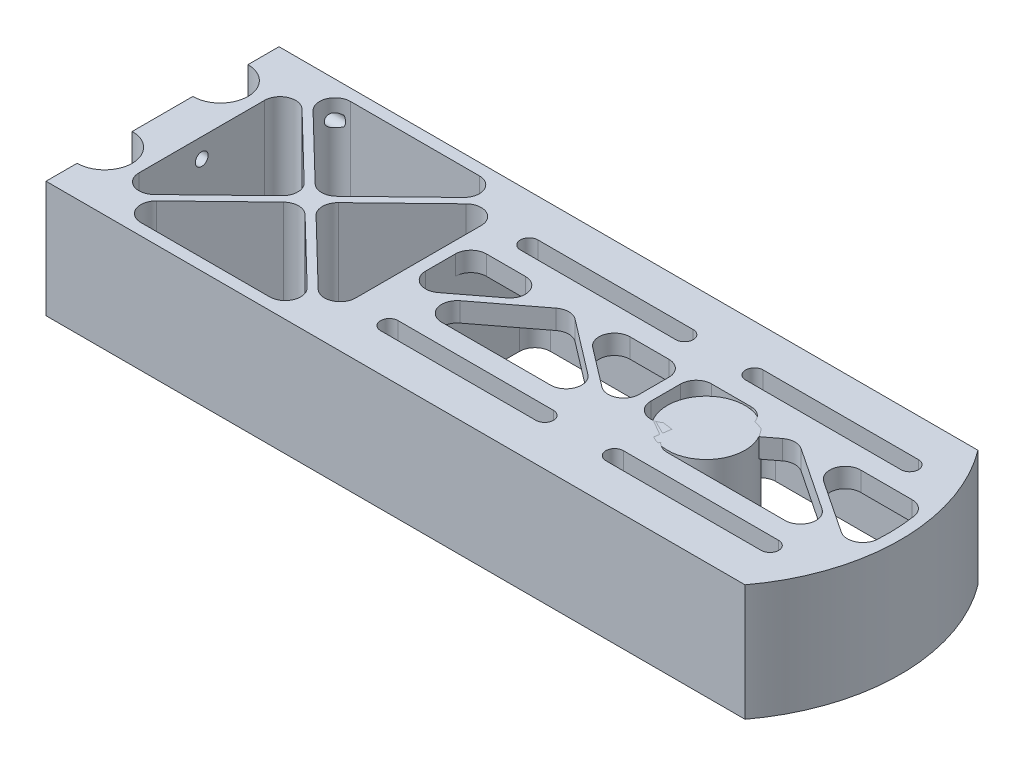
SolidWorks part; units mm, degrees
material "3.1355 (EN-AW 2024)"
ref_plane "Front" through (0, 0, 0) normal (0, 0, 1) x (1, 0, 0)
ref_plane "Top" through (0, 0, 0) normal (0, 1, 0) x (1, 0, 0)
ref_plane "Right" through (0, 0, 0) normal (1, 0, 0) x (0, 0, -1)
sketch "Эскиз1" plane through (0, 0, 0) normal (0, 1, 0) x (1, 0, 0)
  line L0 (0, 0) -> (0, 60) construction
  line L1 (0, 60) -> (180, 60)
  line L2 (190, 60) -> (190, 0) construction
  line L3 (190, 0) -> (180, 0) construction
  line L4 (0, 30) -> (140, 30) construction
  line L5 (0, 60) -> (0, 52)
  line L6 (0, 37.8) -> (0, 22.2)
  line L7 (0, 8) -> (0, 0)
  line L8 (140, 30) -> (190, 30) construction
  line L9 (180, 60) -> (190, 60) construction
  line L10 (180, 0) -> (0, 0)
  circle A0 centre (0, 44.9) radius 7.1 construction
  circle A1 centre (0, 15.1) radius 7.1 construction
  arc A2 (0, 52) -> (0, 37.8) centre (0, 44.9) cw
  arc A3 (0, 8) -> (0, 22.2) centre (0, 15.1) ccw
  arc A4 (180, 0) -> (180, 60) centre (140, 30) ccw
  point P11 (0, 52)
  point P12 (0, 37.8)
  dimension "D2" = 14.2
  dimension "D4" = 29.8
  dimension "D8" = 50
  dimension "D1" = 60
  dimension "D3" = 15.1
  dimension "D5" = 140
  dimension "D6" = 50
  dimension "D7" = 190
extrude "Бобышка-Вытянуть1" add sketch "Эскиз1" along normal blind 30
sketch "Эскиз2" plane through (0, 30, 0) normal (0, 1, 0) x (1, 0, 0)
  line L5 (3, 3) -> (178.4708, 3)
  line L6 (3, 3) -> (178.4708, 3)
  line L12 (3, 5.4558) -> (3, 3)
  line L15 (178.4708, 57) -> (3, 57)
  line L16 (3, 57) -> (3, 54.5442)
  line L17 (3, 35.2558) -> (3, 24.7442)
  line L18 (3, 5.4558) -> (3, 3)
  line L21 (178.4708, 57) -> (3, 57)
  line L22 (3, 57) -> (3, 54.5442)
  line L23 (3, 35.2558) -> (3, 24.7442)
  arc A3 (178.4708, 3) -> (178.4708, 57) centre (140, 30) ccw
  arc A4 (3, 35.2558) -> (3, 54.5442) centre (0, 44.9) ccw
  arc A5 (3, 5.4558) -> (3, 24.7442) centre (0, 15.1) ccw
  arc A6 (3, 35.2558) -> (3, 54.5442) centre (0, 44.9) ccw
  arc A7 (3, 5.4558) -> (3, 24.7442) centre (0, 15.1) ccw
  arc A8 (178.4708, 3) -> (178.4708, 57) centre (140, 30) ccw
  dimension "D1" = 3
extrude "Вырез-Вытянуть1" cut sketch "Эскиз2" against normal through all
sketch "Temp" plane through (0, 30, 0) normal (0, 1, 0) x (1, 0, 0)
  circle A0 centre (140, 30) radius 10
  dimension "D1" = 20
extrude "Бобышка-Вытянуть2" add sketch "Temp" against normal up to surface (30 mm away) separate body up to face at (49.7088, 0, -30)
sketch "Эскиз3" plane through (0, 30, 0) normal (0, 1, 0) x (1, 0, 0)
  line L0 (178.4708, 57) -> (3, 57) construction
  line L1 (174.4166, 48) -> (134.4166, 48) construction
  line L2 (174.4166, 43.5) -> (134.4166, 43.5)
  line L3 (174.4166, 52.5) -> (134.4166, 52.5)
  line L4 (174.4166, 48) -> (183.4166, 48) construction
  line L5 (125.4166, 57) -> (125.4166, 30) construction
  line L6 (0, 30) -> (140, 30) construction
  line L7 (76.4166, 48) -> (116.4166, 48) construction
  line L8 (76.4166, 43.5) -> (116.4166, 43.5)
  line L9 (76.4166, 52.5) -> (116.4166, 52.5)
  line L10 (187, 30) -> (125.4166, 30) construction
  line L11 (76.4166, 12) -> (116.4166, 12) construction
  line L12 (76.4166, 16.5) -> (116.4166, 16.5)
  line L13 (76.4166, 7.5) -> (116.4166, 7.5)
  line L14 (174.4166, 12) -> (134.4166, 12) construction
  line L15 (174.4166, 16.5) -> (134.4166, 16.5)
  line L16 (174.4166, 7.5) -> (134.4166, 7.5)
  line L17 (68.9166, 57) -> (68.9166, 40.5)
  line L18 (68.9166, 40.5) -> (185.8121, 40.5)
  line L19 (178.4708, 57) -> (68.9166, 57)
  line L20 (76.4166, 12) -> (116.4166, 12) construction
  line L21 (76.4166, 16.5) -> (116.4166, 16.5)
  line L22 (76.4166, 7.5) -> (116.4166, 7.5)
  line L23 (174.4166, 12) -> (134.4166, 12) construction
  line L24 (174.4166, 16.5) -> (134.4166, 16.5)
  line L25 (174.4166, 7.5) -> (134.4166, 7.5)
  line L26 (68.9166, 19.5) -> (185.8121, 19.5)
  line L27 (178.4708, 3) -> (68.9166, 3)
  line L28 (68.9166, 3) -> (68.9166, 19.5)
  arc A0 (174.4166, 43.5) -> (174.4166, 52.5) centre (174.4166, 48) ccw
  arc A1 (134.4166, 52.5) -> (134.4166, 43.5) centre (134.4166, 48) ccw
  arc A2 (178.4708, 3) -> (178.4708, 57) centre (140, 30) ccw construction
  arc A3 (76.4166, 43.5) -> (76.4166, 52.5) centre (76.4166, 48) cw
  arc A4 (116.4166, 52.5) -> (116.4166, 43.5) centre (116.4166, 48) cw
  arc A5 (76.4166, 16.5) -> (76.4166, 7.5) centre (76.4166, 12) ccw
  arc A6 (116.4166, 7.5) -> (116.4166, 16.5) centre (116.4166, 12) ccw
  arc A7 (174.4166, 16.5) -> (174.4166, 7.5) centre (174.4166, 12) cw
  arc A8 (134.4166, 7.5) -> (134.4166, 16.5) centre (134.4166, 12) cw
  arc A9 (185.8121, 40.5) -> (178.4708, 57) centre (140, 30) ccw
  arc A10 (76.4166, 16.5) -> (76.4166, 7.5) centre (76.4166, 12) ccw
  arc A11 (116.4166, 7.5) -> (116.4166, 16.5) centre (116.4166, 12) ccw
  arc A12 (174.4166, 16.5) -> (174.4166, 7.5) centre (174.4166, 12) cw
  arc A13 (134.4166, 7.5) -> (134.4166, 16.5) centre (134.4166, 12) cw
  arc A14 (185.8121, 19.5) -> (178.4708, 3) centre (140, 30) cw
  point P1 (154.4166, 48)
  point P20 (96.4166, 48)
  point P28 (96.4166, 12)
  point P35 (154.4166, 12)
  arc M3 (178.4708, 57) -> (178.4708, 3) centre (140, 30) cw
  line M4 (178.4708, 3) -> (3, 3)
  line M10 (3, 57) -> (178.4708, 57)
  dimension "D1" = 4.5
  dimension "D6" = 3
  dimension "D2" = 40
  dimension "D3" = 9
  dimension "D4" = 9
  dimension "D5" = 9
  dimension "D7" = 7.5
extrude "Бобышка-Вытянуть3" add sketch "Эскиз3" against normal blind 5 contours L17 L18 A1 L3 A0 L2 L9 A4 L8 A3 M3 M10 | L28 L26 A6 L13 A5 L12 L16 A8 L15 A7 M4 M3
sketch "Эскиз4" plane through (0, 30, 0) normal (0, 1, 0) x (1, 0, 0)
  line L0 (3, 57) -> (3, 54.5442) construction
  line L1 (3, 35.2558) -> (3, 24.7442) construction
  line L2 (3, 5.4558) -> (3, 3) construction
  line L3 (3, 3) -> (68.9166, 3) construction
  line L4 (68.9166, 57) -> (3, 57) construction
  line L5 (3, 57) -> (3, 54.5442)
  line L6 (3, 35.2558) -> (3, 24.7442)
  line L7 (3, 5.4558) -> (3, 3)
  line L8 (3, 3) -> (10.1, 3)
  line L9 (10.1, 57) -> (3, 57)
  line L10 (10.1, 57) -> (10.1, 3)
  arc A0 (3, 35.2558) -> (3, 54.5442) centre (0, 44.9) ccw construction
  arc A1 (3, 5.4558) -> (3, 24.7442) centre (0, 15.1) ccw construction
  arc A2 (3, 35.2558) -> (3, 54.5442) centre (0, 44.9) ccw
  arc A3 (3, 5.4558) -> (3, 24.7442) centre (0, 15.1) ccw
  line M4 (68.9166, 3) -> (3, 3)
  line M5 (3, 3) -> (3, 5.4558)
  arc M6 (3, 5.4558) -> (3, 24.7442) centre (0, 15.1) ccw
  line M7 (3, 24.7442) -> (3, 35.2558)
  arc M8 (3, 35.2558) -> (3, 54.5442) centre (0, 44.9) ccw
  line M9 (3, 54.5442) -> (3, 57)
  line M10 (3, 57) -> (68.9166, 57)
extrude "Бобышка-Вытянуть4" add sketch "Эскиз4" against normal through all contours L10 M10 M9 M8 | L10 M8 M7 M6 | L10 M6 M5 M4
sketch "Эскиз6" plane through (0, 30, 0) normal (0, 1, 0) x (1, 0, 0)
  line L0 (65.9166, 57) -> (65.9166, 3)
  line L1 (68.9166, 57) -> (10.1, 57) construction
  line L2 (10.1, 3) -> (68.9166, 3) construction
  line L3 (68.9166, 57) -> (68.9166, 40.5) construction
  line L4 (65.9166, 3) -> (68.9166, 3)
  line L5 (68.9166, 3) -> (68.9166, 57)
  line L6 (68.9166, 57) -> (65.9166, 57)
  dimension "D1" = 3
extrude "Бобышка-Вытянуть5" add sketch "Эскиз6" against normal through all
sketch "Эскиз7" plane through (0, 30, 0) normal (0, 1, 0) x (1, 0, 0)
  line L0 (10.1, 3) -> (65.9166, 57) construction
  line L1 (10.1, 57) -> (65.9166, 3) construction
  line L2 (10.1, 55.6086) -> (36.5701, 30)
  line L3 (11.5382, 3) -> (38.0083, 28.6086)
  line L4 (11.5382, 57) -> (38.0083, 31.3914)
  line L5 (10.1, 4.3914) -> (36.5701, 30)
  line L6 (65.9166, 57) -> (10.1, 57) construction
  line L7 (10.1, 57) -> (10.1, 3) construction
  line L8 (10.1, 3) -> (65.9166, 3) construction
  line L9 (65.9166, 57) -> (65.9166, 3) construction
  line L10 (65.9166, 57) -> (64.4784, 57)
  line L11 (10.1, 57) -> (10.1, 55.6086)
  line L12 (10.1, 3) -> (11.5382, 3)
  line L13 (65.9166, 57) -> (65.9166, 55.6086)
  line L14 (11.5382, 57) -> (10.1, 57)
  line L15 (10.7953, 57.7187) -> (66.6119, 3.7187) construction
  line L16 (9.4047, 56.2813) -> (65.2213, 2.2813) construction
  line L17 (65.9166, 4.3914) -> (65.9166, 3)
  line L18 (9.4047, 3.7187) -> (65.2213, 57.7187) construction
  line L19 (10.7953, 2.2813) -> (66.6119, 56.2813) construction
  line L20 (64.4784, 3) -> (65.9166, 3)
  line L21 (10.1, 4.3914) -> (10.1, 3)
  line L22 (39.4465, 30) -> (65.9166, 55.6086)
  line L23 (39.4465, 30) -> (65.9166, 4.3914)
  line L24 (38.0083, 31.3914) -> (64.4784, 57)
  line L25 (38.0083, 28.6086) -> (64.4784, 3)
  dimension "D1" = 1
  dimension "D2" = 1
extrude "Бобышка-Вытянуть6" add sketch "Эскиз7" against normal through all
sketch "Эскиз9" plane through (0, 25, 0) normal (0, -1, 0) x (1, 0, 0)
  line L0 (120.9166, -12) -> (129.9166, -12) construction
  line L1 (125.4166, -3) -> (125.4166, -57) construction
  line L2 (68.9166, -57) -> (178.4708, -57) construction
  line L3 (123.9166, -3) -> (123.9166, -57)
  line L4 (101.5292, -3) -> (68.9166, -3) construction
  line L5 (126.9166, -3) -> (126.9166, -57)
  line L6 (123.9166, -3) -> (126.9166, -3)
  line L7 (123.9166, -57) -> (126.9166, -57)
  arc A0 (116.4166, -16.5) -> (116.4166, -7.5) centre (116.4166, -12) ccw construction
  arc A1 (134.4166, -16.5) -> (134.4166, -7.5) centre (134.4166, -12) ccw construction
  point P8 (125.4166, -12)
  dimension "D1" = 1.5
  dimension "D2" = 1.5
extrude "Бобышка-Вытянуть8" add sketch "Эскиз9" along normal through all and the other way through all
sketch "Эскиз8" plane through (0, 30, 0) normal (0, 1, 0) x (1, 0, 0)
  line L0 (96.4166, 43.5) -> (96.4166, 16.5) construction
  line L1 (76.4166, 43.5) -> (116.4166, 43.5) construction
  line L2 (76.4166, 16.5) -> (116.4166, 16.5) construction
  line L3 (154.4166, 43.5) -> (154.4166, 16.5) construction
  line L4 (174.4166, 43.5) -> (134.4166, 43.5) construction
  line L5 (174.4166, 16.5) -> (134.4166, 16.5) construction
  line L6 (68.9166, 19.5) -> (96.4166, 40.5) construction
  line L7 (116.4166, 48) -> (134.4166, 48) construction
  line L8 (125.4166, 48) -> (125.4166, 19.5) construction
  line L9 (68.9166, 40.5) -> (123.9166, 40.5) construction
  line L10 (96.4166, 40.5) -> (123.9166, 19.5) construction
  line L11 (126.9166, 19.5) -> (154.4401, 40.4052) construction
  line L12 (154.4401, 40.4052) -> (185.8121, 19.5) construction
  line L13 (70.5643, 19.5) -> (96.4166, 39.2418)
  line L14 (96.4166, 39.2418) -> (122.2689, 19.5)
  line L15 (128.5699, 19.5) -> (154.478, 39.1782)
  line L16 (154.478, 39.1782) -> (184.0088, 19.5)
  line L17 (68.9166, 20.7582) -> (94.7689, 40.5)
  line L18 (98.0643, 40.5) -> (123.9166, 20.7582)
  line L19 (126.9166, 20.7557) -> (152.9116, 40.5)
  line L20 (122.2689, 19.5) -> (123.9166, 19.5)
  line L22 (94.7689, 40.5) -> (98.0643, 40.5)
  line L23 (68.9166, 19.5) -> (68.9166, 40.5) construction
  line L24 (68.9166, 19.5) -> (123.9166, 19.5) construction
  line L25 (123.9166, 19.5) -> (123.9166, 40.5) construction
  line L26 (126.9166, 40.5) -> (126.9166, 19.5) construction
  line L27 (126.9166, 40.5) -> (185.8121, 40.5) construction
  line L28 (126.9166, 19.5) -> (185.8121, 19.5) construction
  line L29 (68.9166, 19.5) -> (68.9166, 20.7582)
  line L30 (68.9166, 19.5) -> (70.5643, 19.5)
  line L31 (123.9166, 19.5) -> (123.9166, 20.7582)
  line L32 (126.9166, 20.7557) -> (126.9166, 19.5)
  line L33 (152.9116, 40.5) -> (156.1011, 40.5)
  line L34 (126.9166, 19.5) -> (128.5699, 19.5)
  line L35 (184.0088, 19.5) -> (185.8121, 19.5)
  line L36 (154.4021, 41.6321) -> (186.3666, 20.3322) construction
  line L37 (154.478, 39.1782) -> (185.2576, 18.6678) construction
  line L38 (156.1011, 40.5) -> (186.0401, 20.5497)
  line L39 (127.5214, 18.7037) -> (154.478, 39.1782) construction
  line L40 (126.3117, 20.2963) -> (154.4021, 41.6321) construction
  line L42 (96.4166, 41.7582) -> (124.5235, 20.2948) construction
  line L43 (68.3097, 20.2948) -> (96.4166, 41.7582) construction
  line L44 (69.5235, 18.7052) -> (96.4166, 39.2418) construction
  line L45 (96.4166, 39.2418) -> (123.3097, 18.7052) construction
  arc A1 (185.8121, 19.5) -> (185.8121, 40.5) centre (140, 30) ccw construction
  arc A2 (185.8121, 19.5) -> (186.0401, 20.5497) centre (140, 30) ccw
  point P26 (69.5235, 18.7052)
  point P27 (96.4324, 39.2539)
  point P28 (125.4324, 18.2539)
  point P30 (185.2357, 18.6828)
  point P31 (68.3097, 20.2948)
  point P32 (96.4007, 41.7461)
  point P33 (125.4007, 20.7461)
  point P34 (154.3931, 42.8858)
  point P35 (186.3885, 20.3172)
  point P49 (154.4166, 40.5)
  dimension "D1" = 1
  dimension "D2" = 1
extrude "Бобышка-Вытянуть7" add sketch "Эскиз8" against normal up to surface (5 mm away) up to face at (96.4166, 25, -12)
fillet "Скругление1" radius 4 12 edges at (11.5382, 15, -57) (38.0083, 15, -31.3914) (64.4784, 15, -57) (65.9166, 15, -55.6086) (39.4465, 15, -30) (65.9166, 15, -4.3914) (11.5382, 15, -3) (64.4784, 15, -3) (38.0083, 15, -28.6086) (10.1, 15, -4.3914) (36.5701, 15, -30) (10.1, 15, -55.6086)
fillet "Скругление2" radius 4 8 edges at (178.4708, 12.5, -57) (178.4708, 12.5, -3) (126.9166, 12.5, -3) (126.9166, 12.5, -57) (123.9166, 12.5, -3) (68.9166, 12.5, -3) (68.9166, 12.5, -57) (123.9166, 12.5, -57)
fillet "Скругление3" radius 4 18 edges at (98.0643, 27.5, -40.5) (123.9166, 27.5, -40.5) (123.9166, 27.5, -20.7582) (122.2689, 27.5, -19.5) (96.4166, 27.5, -39.2418) (70.5643, 27.5, -19.5) (94.7689, 27.5, -40.5) (68.9166, 27.5, -40.5) (68.9166, 27.5, -20.7582) (185.8121, 27.5, -40.5) (156.1011, 27.5, -40.5) (186.0401, 27.5, -20.5497) (184.0088, 27.5, -19.5) (154.478, 27.5, -39.1782) (128.5699, 27.5, -19.5) (126.9166, 27.5, -20.7557) (152.9116, 27.5, -40.5) (126.9166, 27.5, -40.5)
sketch "Эскиз10" plane through (0, 30, 0) normal (0, 1, 0) x (1, 0, 0)
  line L90 (76.4166, 52.5) -> (116.4166, 52.5) construction
  line L91 (76.4166, 43.5) -> (116.4166, 43.5) construction
  line L92 (116.4166, 50.25) -> (76.4166, 50.25)
  line L93 (76.4166, 45.75) -> (116.4166, 45.75)
  line L94 (116.4166, 50.25) -> (76.4166, 50.25)
  line L95 (76.4166, 45.75) -> (116.4166, 45.75)
  line L96 (76.4166, 52.5) -> (116.4166, 52.5)
  line L97 (76.4166, 43.5) -> (116.4166, 43.5)
  line L98 (174.4166, 52.5) -> (134.4166, 52.5) construction
  line L99 (174.4166, 43.5) -> (134.4166, 43.5) construction
  line L100 (174.4166, 52.5) -> (134.4166, 52.5)
  line L101 (174.4166, 43.5) -> (134.4166, 43.5)
  line L102 (76.4166, 16.5) -> (116.4166, 16.5) construction
  line L103 (76.4166, 7.5) -> (116.4166, 7.5) construction
  line L104 (76.4166, 16.5) -> (116.4166, 16.5)
  line L105 (76.4166, 7.5) -> (116.4166, 7.5)
  line L106 (174.4166, 16.5) -> (134.4166, 16.5) construction
  line L107 (174.4166, 7.5) -> (134.4166, 7.5) construction
  line L108 (174.4166, 16.5) -> (134.4166, 16.5)
  line L109 (174.4166, 7.5) -> (134.4166, 7.5)
  line L110 (174.4166, 45.75) -> (134.4166, 45.75)
  line L111 (174.4166, 50.25) -> (134.4166, 50.25)
  line L112 (174.4166, 14.25) -> (134.4166, 14.25)
  line L113 (174.4166, 9.75) -> (134.4166, 9.75)
  line L114 (76.4166, 9.75) -> (116.4166, 9.75)
  line L115 (76.4166, 14.25) -> (116.4166, 14.25)
  arc A90 (76.4166, 52.5) -> (76.4166, 43.5) centre (76.4166, 48) ccw construction
  arc A91 (116.4166, 43.5) -> (116.4166, 52.5) centre (116.4166, 48) ccw construction
  arc A92 (76.4166, 50.25) -> (76.4166, 45.75) centre (76.4166, 48) ccw
  arc A93 (116.4166, 45.75) -> (116.4166, 50.25) centre (116.4166, 48) ccw
  arc A94 (76.4166, 50.25) -> (76.4166, 45.75) centre (76.4166, 48) ccw
  arc A95 (116.4166, 45.75) -> (116.4166, 50.25) centre (116.4166, 48) ccw
  arc A96 (76.4166, 52.5) -> (76.4166, 43.5) centre (76.4166, 48) ccw
  arc A97 (116.4166, 43.5) -> (116.4166, 52.5) centre (116.4166, 48) ccw
  arc A98 (134.4166, 52.5) -> (134.4166, 43.5) centre (134.4166, 48) ccw construction
  arc A99 (174.4166, 43.5) -> (174.4166, 52.5) centre (174.4166, 48) ccw construction
  arc A100 (134.4166, 52.5) -> (134.4166, 43.5) centre (134.4166, 48) ccw
  arc A101 (174.4166, 43.5) -> (174.4166, 52.5) centre (174.4166, 48) ccw
  arc A102 (116.4166, 7.5) -> (116.4166, 16.5) centre (116.4166, 12) ccw construction
  arc A103 (76.4166, 16.5) -> (76.4166, 7.5) centre (76.4166, 12) ccw construction
  arc A104 (116.4166, 7.5) -> (116.4166, 16.5) centre (116.4166, 12) ccw
  arc A105 (76.4166, 16.5) -> (76.4166, 7.5) centre (76.4166, 12) ccw
  arc A106 (134.4166, 16.5) -> (134.4166, 7.5) centre (134.4166, 12) ccw construction
  arc A107 (174.4166, 7.5) -> (174.4166, 16.5) centre (174.4166, 12) ccw construction
  arc A108 (134.4166, 16.5) -> (134.4166, 7.5) centre (134.4166, 12) ccw
  arc A109 (174.4166, 7.5) -> (174.4166, 16.5) centre (174.4166, 12) ccw
  arc A110 (134.4166, 50.25) -> (134.4166, 45.75) centre (134.4166, 48) ccw
  arc A111 (174.4166, 45.75) -> (174.4166, 50.25) centre (174.4166, 48) ccw
  arc A112 (134.4166, 14.25) -> (134.4166, 9.75) centre (134.4166, 12) ccw
  arc A113 (174.4166, 9.75) -> (174.4166, 14.25) centre (174.4166, 12) ccw
  arc A114 (76.4166, 14.25) -> (76.4166, 9.75) centre (76.4166, 12) ccw
  arc A115 (116.4166, 9.75) -> (116.4166, 14.25) centre (116.4166, 12) ccw
  dimension "D1" = 2.25
  dimension "D2" = 2.25
  dimension "D3" = 2.25
  dimension "D4" = 2.25
extrude "Бобышка-Вытянуть9" add sketch "Эскиз10" against normal up to surface (5 mm away) up to face at (155.2427, 25, -27.7696)
sketch "Эскиз12" plane through (0, 0, 0) normal (0, -1, 0) x (1, 0, 0)
  line L0 (5, -23.8755) -> (5, -36.1245)
  line L1 (0, -37.8) -> (0, -22.2) construction
  line L2 (10.1, -46.1732) -> (10.1, -13.8268) construction
  line L3 (10.1, -44.9) -> (10.1, -15.1)
  arc A6 (0, -25.2) -> (0, -5) centre (0, -15.1) ccw
  arc A7 (5, -23.8755) -> (10.1, -15.1) centre (0, -15.1) ccw
  arc A9 (0, -55) -> (0, -34.8) centre (0, -44.9) ccw
  arc A10 (10.1, -44.9) -> (5, -36.1245) centre (0, -44.9) ccw
  dimension "D3" = 5
  dimension "D1" = 3
  dimension "D2" = 3
extrude "Вырез-Вытянуть2" [suppressed] cut sketch "Эскиз12" against normal through all
hole_wizard "Отверстие обработанное метчиком M4x0.71" positions "Эскиз13" profile "Эскиз14" tap size "M4x0.7" standard "Ansi Metric"
sketch "Эскиз13" plane through (0, -175.3797, -75.0604) normal (-1, 0, 0) x (0, 0, 1)
  point P0 (19.3104, 200.3797)
  point P3 (45.0604, 200.3797)
  point P6 (70.8104, 200.3797)
  point P9 (70.8104, 180.3797)
  point P12 (45.0604, 180.3797)
  point P15 (19.3104, 180.3797)
sketch "Эскиз14" plane through (0, 25, -55.75) normal (0, 1, 0) x (0, 0, 1)
  line L0 (0, 0) -> (0, 20.9914)
  line L1 (0, 20.9914) -> (1.65, 20)
  line L2 (1.65, 20) -> (1.65, 0)
  line L3 (1.65, 0) -> (0, 0)
  line L4 (0, 20.9914) -> (-1.65, 20) construction
  line L5 (0, -6.35) -> (0, 107.95) construction
  dimension "Диаметр сверла" = 3.3
  dimension "Глубина сверла" = 20
  dimension "Угол заточки сверла" = 118
cosmetic thread "Отверстие резьбы1" parameters "D1"=8, "D2"=4
cosmetic thread "Отверстие резьбы2" parameters "D1"=8, "D2"=4
cosmetic thread "Отверстие резьбы3" parameters "D1"=8, "D2"=4
cosmetic thread "Отверстие резьбы4" parameters "D1"=8, "D2"=4
cosmetic thread "Отверстие резьбы5" parameters "D1"=8, "D2"=4
cosmetic thread "Отверстие резьбы6" parameters "D1"=8, "D2"=4
sketch "Эскиз15" [suppressed] plane through (0, 0, 0) normal (0, -1, 0) x (1, 0, 0)
  line L5 (180, 0) -> (0, 0)
  line L6 (0, 0) -> (0, -8)
  line L7 (0, -22.2) -> (0, -37.8)
  line L8 (0, -52) -> (0, -60)
  line L9 (0, -60) -> (180, -60)
  line L10 (180, 0) -> (0, 0)
  line L11 (0, 0) -> (0, -8)
  line L12 (0, -22.2) -> (0, -37.8)
  line L13 (0, -52) -> (0, -60)
  line L14 (0, -60) -> (180, -60)
  arc A3 (0, -22.2) -> (0, -8) centre (0, -15.1) ccw
  arc A4 (0, -52) -> (0, -37.8) centre (0, -44.9) ccw
  arc A5 (180, -60) -> (180, 0) centre (140, -30) ccw
  arc A6 (0, -22.2) -> (0, -8) centre (0, -15.1) ccw
  arc A7 (0, -52) -> (0, -37.8) centre (0, -44.9) ccw
  arc A8 (180, -60) -> (180, 0) centre (140, -30) ccw
  dimension "D1" = 0
extrude "Вырез-Вытянуть3" [suppressed] cut sketch "Эскиз15" against normal blind 20
split "Разделить1" [suppressed] bodies to split 113
move or copy body "Тело-Переместить/Копировать1" [suppressed] bodies to move or copy 116 placed by mates yes
other "Расстояние2" [suppressed] parameters "D1"=50
equation "\"D3@Эскиз1\"=8+\"D2@Эскиз1\"/2"
equation "\"D7@Эскиз3\"=\"D1@Эскиз3\"+3"
